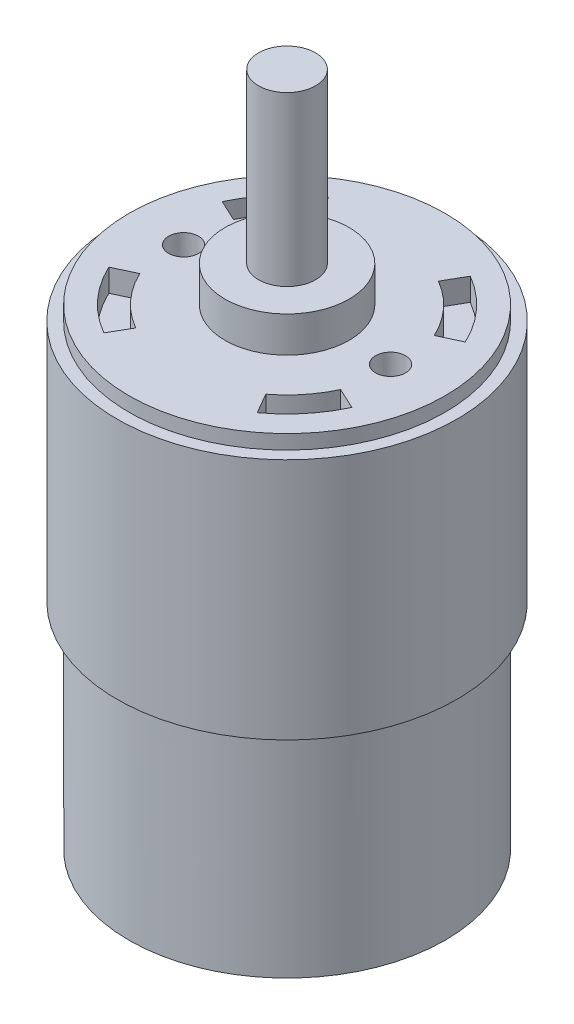
SolidWorks part; units mm, degrees
ref_plane "Front Plane" through (0, 0, 0) normal (0, 0, 1) x (1, 0, 0)
ref_plane "Top Plane" through (0, 0, 0) normal (0, 1, 0) x (1, 0, 0)
ref_plane "Right Plane" through (0, 0, 0) normal (1, 0, 0) x (0, 0, -1)
sketch "Sketch2" plane through (0, 0, 0) normal (0, 1, 0) x (1, 0, 0)
  circle A0 centre (0, 0) radius 22.1488
  dimension "D1" = 44.2976
extrude "Boss-Extrude4" add sketch "Sketch2" along normal blind 66.0908
sketch "Sketch4" plane through (0, 66.0908, 0) normal (0, 1, 0) x (1, 0, 0)
  circle A0 centre (0, 0) radius 8.6995
  dimension "D1" = 17.399
extrude "Boss-Extrude5" add sketch "Sketch4" along normal blind 5.0038 contours A0
sketch "Sketch9" plane through (0, 71.0946, 0) normal (0, 1, 0) x (1, 0, 0)
  circle A0 centre (0, 0) radius 4.0005
  dimension "D1" = 8.001
extrude "Boss-Extrude6" add sketch "Sketch9" along normal blind 23.5458
sketch "Sketch10" plane through (0, 0, 0) normal (0, -1, 0) x (1, 0, 0)
  circle A0 centre (0, 0) radius 8.7503
  dimension "D1" = 17.5006
extrude "Boss-Extrude7" add sketch "Sketch10" along normal blind 6.7056
sketch "Sketch11" plane through (0, -6.7056, 0) normal (0, -1, 0) x (1, 0, 0)
  circle A0 centre (0, 0) radius 2.5019
  dimension "D1" = 5.0038
extrude "Boss-Extrude8" add sketch "Sketch11" along normal blind 2.413
ref_plane "Plane2" through (0, 64.0842, 0) normal (0, -1, 0) x (-1, 0, 0)
sketch "Sketch12" plane through (0, 64.0842, 0) normal (0, -1, 0) x (-1, 0, 0)
  circle A0 centre (0, 0) radius 23.8125
  dimension "D1" = 47.625
extrude "Boss-Extrude9" add sketch "Sketch12" along normal blind 34.0106
sketch "Sketch13" plane through (0, 66.0908, 0) normal (0, 1, 0) x (1, 0, 0)
  line L0 (-29.6451, 0) -> (29.6451, 0) construction
  line L1 (0, -27.354) -> (0, 29.9922) construction
  circle A0 centre (-14.5034, 0) radius 2.0955
  circle A1 centre (0, 0) radius 14.5034 construction
  circle A2 centre (14.5034, 0) radius 2.0955
  dimension "D1" = 4.191
  dimension "D2" = 29.0068
extrude "Cut-Extrude1" cut sketch "Sketch13" against normal blind 3.175
sketch "Sketch14" plane through (0, 66.0908, 0) normal (0, 1, 0) x (1, 0, 0)
  line L0 (-17.0333, -7.9428) -> (-14.07, -6.561)
  line L1 (-9.3971, -16.2762) -> (-7.7623, -13.4446)
  line L2 (-24.8296, 0) -> (26.0831, 0) construction
  line L3 (0, -32.9776) -> (0, 32.0133) construction
  line L4 (-17.0333, 7.9428) -> (-14.07, 6.561)
  line L5 (-10.0803, 15.8622) -> (-8.4437, 13.0275)
  line L6 (7.7623, 13.4446) -> (9.3971, 16.2762)
  line L7 (14.07, 6.561) -> (17.0333, 7.9428)
  line L8 (9.3859, -12.3659) -> (11.0315, -15.216)
  line L9 (14.07, -6.561) -> (17.0333, -7.9428)
  circle A0 centre (0, 0) radius 16.306 construction
  circle A1 centre (0, 0) radius 18.7942
  circle A2 centre (0, 0) radius 15.5245
  dimension "D1" = 65
  dimension "D2" = 30
  dimension "D3" = 30
  dimension "D4" = 65
  dimension "D5" = 30
  dimension "D6" = 65
  dimension "D7" = 65
  dimension "D8" = 30
extrude "Cut-Extrude2" cut sketch "Sketch14" against normal blind 3.175 contours A2 L0 A1 L1 | A2 L5 A1 L4 | A2 L7 A1 L6 | A2 L8 A1 L9
sketch "Sketch15" plane through (0, 0, 0) normal (0, -1, 0) x (1, 0, 0)
  circle A0 centre (0, 0) radius 8.7503
  circle A1 centre (0, 0) radius 20.9582
  circle A2 centre (0, 0) radius 22.1488 construction
  dimension "D1" = 1.1906
extrude "Cut-Extrude3" cut sketch "Sketch15" against normal blind 3.175
sketch "Sketch16" plane through (0, -6.7056, 0) normal (0, -1, 0) x (1, 0, 0)
  circle A0 centre (0, 0) radius 2.5019
  circle A1 centre (0, 0) radius 7.1628
  circle A2 centre (0, 0) radius 8.7503 construction
  dimension "D1" = 1.5875
extrude "Cut-Extrude4" cut sketch "Sketch16" against normal blind 2.54
sketch "Sketch18" plane through (0, 0, 0) normal (0, -1, 0) x (1, 0, 0)
  line L1 (20.5261, 3.7465) -> (17.399, 3.7465)
  line L3 (20.7021, -2.6035) -> (17.399, -2.6035)
  line L4 (17.399, 3.7465) -> (17.399, -2.6035)
  circle A0 centre (0, 0) radius 20.8652
  dimension "D1" = 17.399
  dimension "D2" = 6.35
extrude "Boss-Extrude12" add sketch "Sketch18" against normal blind 3.175 contours L3 A0 L1 L4
sketch "Sketch19" plane through (0, 0, 0) normal (0, -1, 0) x (-1, 0, 0)
  line L1 (20.7163, -3.175) -> (17.399, -3.175)
  line L3 (20.7163, 3.175) -> (17.399, 3.175)
  line L4 (17.399, -3.175) -> (17.399, 3.175)
  circle A0 centre (0, 0) radius 20.9582 construction
  arc A1 (20.7163, -3.175) -> (20.7163, 3.175) centre (0, 0) ccw
  dimension "D1" = 6.35
  dimension "D2" = 17.399
extrude "Boss-Extrude13" add sketch "Sketch19" against normal blind 3.175
sketch "Sketch20" plane through (0, 3.175, 0) normal (0, -1, 0) x (-1, 0, 0)
  circle A0 centre (-15.1765, 6.731) radius 1.5875
  dimension "D1" = 3.175
  dimension "D2" = 4.1275
  dimension "D3" = 2.2225
extrude "Cut-Extrude5" cut sketch "Sketch20" against normal blind 3.175
